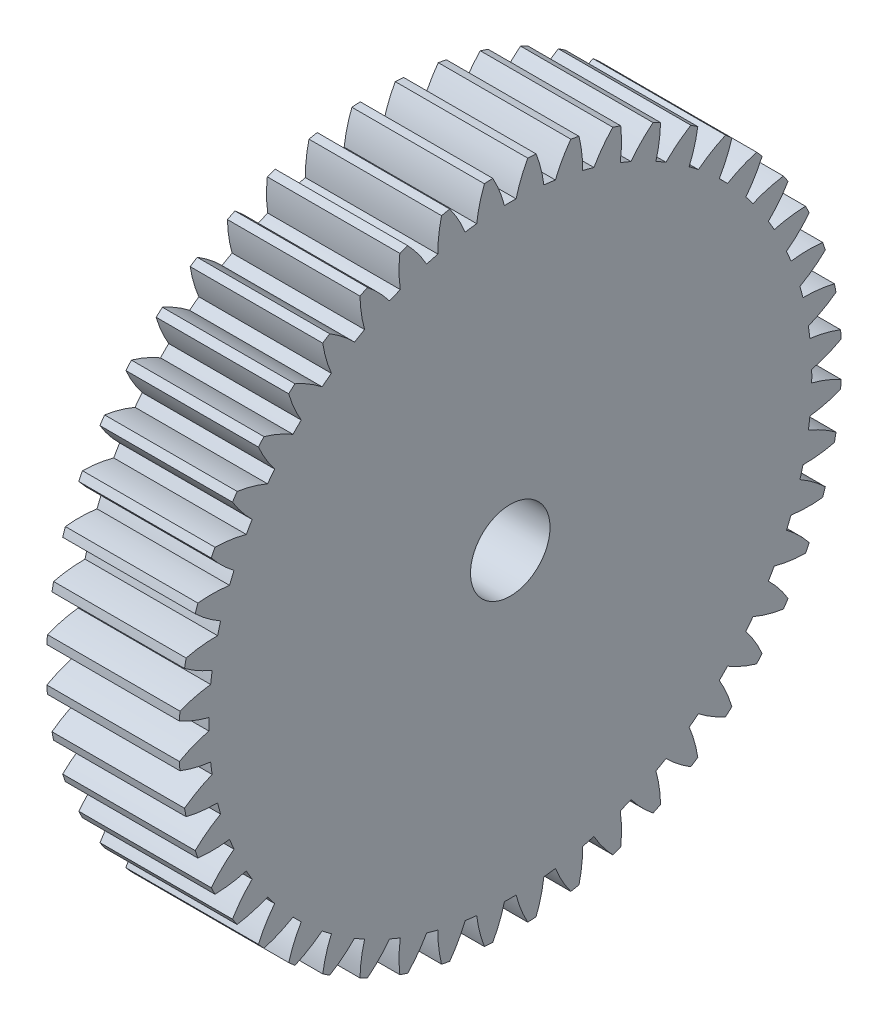
SolidWorks part; units mm, degrees
ref_plane "Plane1" through (0, 0, 0) normal (0, 0, 1) x (1, 0, 0)
ref_plane "Plane2" through (0, 0, 0) normal (0, 1, 0) x (1, 0, 0)
ref_plane "Plane3" through (0, 0, 0) normal (1, 0, 0) x (0, 0, -1)
other "Configuration Table"
sketch "HoldingSke" plane through (0, 0, 0) normal (0, 1, 0) x (1, 0, 0)
  line L0 (0, 0) -> (0.6691, -0.7431)
  line L1 (-15, 0) -> (100, 0) construction
  line L2 (0, 0) -> (-2.1039, 2.3779)
  line L3 (0, 0) -> (-11.863, 4.5341)
  line L4 (0, 0) -> (5.7786, 6.4178)
  line L5 (0, 0) -> (-46.8476, -17.4728)
  line L6 (0, 0) -> (-8.2896, -5.593)
  line L7 (-2.1039, 2.3779) -> (8.6586, 51.2059)
  line L8 (-76.2, 54.61) -> (-75.3, 54.61)
  line L9 (-71.009, 38.7566) -> (-53.1078, 45.2721)
  line L10 (-76.2, 71.12) -> (104.1128, 71.12)
  line L11 (0, 0) -> (-10, 0)
  line L12 (-76.2, 101.6) -> (-76.162, 101.6)
  line L13 (24.9733, 27.94) -> (52.9518, 28.4284)
  line L14 (24.9733, 27.94) -> (24.9743, 27.94)
  line L15 (24.9733, 27.94) -> (100.4006, 29.5858)
  line L16 (-63.627, -1) -> (-12.827, -1)
  circle A0 centre (0, 0) radius 2.5
  circle A1 centre (0, 0) radius 22.749
  circle A2 centre (0, 0) radius 37.5
  circle A3 centre (0, 0) radius 2.5
  dimension "MHD" = 45.498
  dimension "Hub_dia" = 75
  dimension "Bore" = 5
  dimension "MBD" = 5
  dimension "Num_teeth" = 48
  dimension "Pitch" = 1
  dimension "Overall_len" = 50
  dimension "Show_teeth" = 48
  dimension "Thickness" = 10
  dimension "OAL" = 50.0001
  dimension "T_dim" = 0.9
  dimension "Ap" = 20
  dimension "H" = 19.05
  dimension "Pitch_radius" = 180.3128
  dimension "Width" = 10
  dimension "Backlash" = 0.038
  dimension "Addendum_fac" = 1
  dimension "Dedendum_fac" = 1.25
  dimension "Clearance_fac" = 0.25
  dimension "Dedendum_add" = 0.001
  dimension "Module" = 1
sketch "BasProSke" plane through (0, 0, 0) normal (0, 1, 0) x (1, 0, 0)
  line L0 (-10, 0) -> (60, 0) construction
  line L1 (0, 0) -> (0, 25)
  line L2 (0, 0) -> (10, 0)
  line L3 (10, 0) -> (10, 25)
  line L4 (10, 25) -> (0, 25)
  dimension "Thickness" = 10
  dimension "Diameter" = 50
revolve "Base-Revolve" add sketch "BasProSke" angle 360 about L0
sketch "TooCutSke" plane through (0, 0, 0) normal (1, 0, 0) x (0, 0, -1)
  line L1 (0, 0) -> (0, 107) construction
  line L2 (0, 0) -> (-0.8518, 23.9849) construction
  line L3 (0, 0) -> (-3.1379, 47.8757) construction
  line L4 (-0.8518, 23.9849) -> (-1.569, 23.9379) construction
  arc A0 (0.4395, 22.7448) -> (-0.4395, 22.7448) centre (0, 0) ccw
  arc A1 (1.3336, 24.9898) -> (-1.3336, 24.9898) centre (0, 0) ccw
  circle A2 centre (0, 0) radius 24 construction
  circle A3 centre (0, 0) radius 22.5526 construction
  arc A4 (-0.4395, 22.7448) -> (-1.3336, 24.9898) centre (-9.7344, 20.3436) ccw
  arc A5 (1.3336, 24.9898) -> (0.4395, 22.7448) centre (9.7344, 20.3436) ccw
  dimension "Root_dia" = 45.498
  dimension "Overcut_dia" = 50.0508
  dimension "Pitch_dia" = 48
  dimension "Base_dia" = 45.1052
  dimension "Flank_rad" = 9.6
  dimension "Half_ang" = 3.75
  dimension "Half_CT" = 0.7188
extrude "ToothCut" cut sketch "TooCutSke" along normal through all
fillet "Breaks" [suppressed] radius 0.02
fillet "RootFillets" [suppressed] radius 0.251
pattern_circular "TeethCuts" count 48 every 7.5 about axis through (-10, 0, 0) along (1, 0, 0) of "ToothCut", "RootFillets", "Breaks"
sketch "HubNeaOneSke" plane through (0, 0, 0) normal (-1, 0, 0) x (0, 0, 1)
  circle A0 centre (0, 0) radius 22.749
  dimension "Diameter" = 45.498
extrude "HubNearOne" [suppressed] add sketch "HubNeaOneSke" along normal blind 40.0001
sketch "HubNeaBotSke" plane through (0, 0, 0) normal (-1, 0, 0) x (0, 0, 1)
  circle A0 centre (0, 0) radius 22.749
  dimension "Diameter" = 45.498
extrude "HubNearBoth" [suppressed] add sketch "HubNeaBotSke" along normal blind 20
ref_plane "FarPln" through (10, 0, 0) normal (1, 0, 0) x (0, 0, -1)
sketch "HubFarSke" plane through (10, 0, 0) normal (1, 0, 0) x (0, 0, -1)
  circle A0 centre (0, 0) radius 22.749
  dimension "Diameter" = 45.498
extrude "HubFar" [suppressed] add sketch "HubFarSke" along normal blind 20
sketch "BorSke" plane through (0, 0, 0) normal (1, 0, 0) x (0, 0, -1)
  circle A0 centre (0, 0) radius 2.5
  dimension "Diameter" = 5
extrude "Bore" cut sketch "BorSke" along normal mid plane 100.0001
sketch "KeySke" plane through (0, 0, 0) normal (1, 0, 0) x (0, 0, -1)
  line L0 (-1, 0) -> (-1, 3.4)
  line L1 (-1, 3.4) -> (1, 3.4)
  line L2 (1, 3.4) -> (1, 0)
  line L3 (0, 0) -> (0, 34) construction
  line L4 (-1, 0) -> (1, 0)
  dimension "Offset" = 3.4
  dimension "Width" = 2
extrude "Keyway" [suppressed] cut sketch "KeySke" along normal mid plane 100.0001
pattern_circular "Keyway2" [suppressed] count 2 every 90 about axis through (-10, 0, 0) along (1, 0, 0)
sketch "Sketch1" plane through (10, 0, 0) normal (1, 0, 0) x (0, 0, -1)
  circle A0 centre (0, 0) radius 3
  dimension "D1" = 6
extrude "Cut-Extrude1" cut sketch "Sketch1" against normal through all
equation "' \"Module@HoldingSke\" = 6.35"
equation "' \"Num_teeth@HoldingSke\" = 12"
equation "' \"Ap@HoldingSke\" =  20"
equation "' \"Ap@HoldingSke\" = 20"
equation "' \"Width@HoldingSke\" = 0.5 * 25.4"
equation "' \"Hub_dia@HoldingSke\"= 1 * 25.4"
equation "' \"Hub_dia@HoldingSke\" = 1 * 25.4"
equation "' \"Overall_len@HoldingSke\" = 1.0 * 25.4"
equation "' \"Bore@HoldingSke\" = 0.75 * 25.4"
equation "' \"T_dim@HoldingSke\" = 0.1 * 25.4"
equation "' \"Width@KeySke\" = 0.25 * 25.4"
equation "' \"Show_teeth@HoldingSke\" = 13"
equation "' \"Backlash@HoldingSke\" = 0.009 * 25.4"
equation "' \"Addendum_fac@HoldingSke\" = 1.0"
equation "' \"Dedendum_fac@HoldingSke\" = 1.25"
equation "' \"Dedendum_add@HoldingSke\" = 0.00005 * 25.4"
equation "' \"Clearance_fac@HoldingSke\" = 0.25"
equation "\"Pitch@HoldingSke\" = 1 / \"Module@HoldingSke\""
equation "\"Overcut_dia@TooCutSke\" = (\"Num_teeth@HoldingSke\" + 2 * \"Addendum_fac@HoldingSke\") / \"Pitch@HoldingSke\" + 0.002 * 25.4"
equation "\"Pitch_dia@TooCutSke\" = \"Num_teeth@HoldingSke\" / \"Pitch@HoldingSke\""
equation "\"Base_dia@TooCutSke\" = \"Num_teeth@HoldingSke\" / \"Pitch@HoldingSke\" * cos((\"Ap@HoldingSke\"  * 3.14159265 / 180))"
equation "\"Root_dia@TooCutSke\" = (\"Num_teeth@HoldingSke\" + 2) / \"Pitch@HoldingSke\" - 2 * (\"Addendum_fac@HoldingSke\" + \"Dedendum_fac@HoldingSke\") / \"Pitch@HoldingSke\" - \"Dedendum_add@HoldingSke\" * 2"
equation "\"Half_ang@TooCutSke\" = 180 / \"Num_teeth@HoldingSke\""
equation "\"Half_CT@TooCutSke\" = \"Num_teeth@HoldingSke\" / \"Pitch@HoldingSke\" * sin((3.14159265 / 2 / \"Num_teeth@HoldingSke\")) / 2 - 7 * \"Backlash@HoldingSke\" / 4"
equation "\"Flank_rad@TooCutSke\" = \"Num_teeth@HoldingSke\" / \"Pitch@HoldingSke\" / 5"
equation "\"Radius@RootFillets\" = \"Clearance_fac@HoldingSke\" / \"Pitch@HoldingSke\" + \"Dedendum_add@HoldingSke\""
equation "\"Break_rad@Breaks\" = 0.02 / \"Pitch@HoldingSke\""
equation "\"Thickness@HoldingSke\" = \"Width@HoldingSke\""
equation "\"OAL@HoldingSke\" = \"Thickness@HoldingSke\""
equation "\"MHD@HoldingSke\" = (\"Num_teeth@HoldingSke\" + 2) / \"Pitch@HoldingSke\" - 2 * (\"Addendum_fac@HoldingSke\" + \"Dedendum_fac@HoldingSke\")  / \"Pitch@HoldingSke\" - \"Dedendum_add@HoldingSke\" * 2"
equation "\"MBD@HoldingSke\" = (\"Num_teeth@HoldingSke\" + 2) / \"Pitch@HoldingSke\" - 2 * (\"Addendum_fac@HoldingSke\" + \"Dedendum_fac@HoldingSke\")  / \"Pitch@HoldingSke\" - \"Dedendum_add@HoldingSke\" * 2 - 0.002 * 25.4"
equation "\"MHD@HoldingSke\" = ((sgn( \"MHD@HoldingSke\" - \"Hub_dia@HoldingSke\" )-1)*( \"MHD@HoldingSke\" - \"Hub_dia@HoldingSke\" ))/-2+ \"Hub_dia@HoldingSke\""
equation "\"MBD@HoldingSke\" = ((sgn( \"MBD@HoldingSke\" - \"Bore@HoldingSke\" )-1)*( \"MBD@HoldingSke\" - \"Bore@HoldingSke\" ))/-2+ \"Bore@HoldingSke\""
equation "\"OAL@HoldingSke\" = ((sgn( \"OAL@HoldingSke\" - \"Overall_len@HoldingSke\" )+1)*( \"OAL@HoldingSke\" - \"Overall_len@HoldingSke\" ))/2 + \"Overall_len@HoldingSke\" + 0.000002 * 25.4"
equation "\"Num_teeth@TeethCuts\" = int( \"Show_teeth@HoldingSke\" ) + 1"
equation "\"Num_teeth@TeethCuts\" = ((sgn( \"Num_teeth@TeethCuts\" - \"Num_teeth@HoldingSke\" )-1)*( \"Num_teeth@TeethCuts\" - \"Num_teeth@HoldingSke\" ))/-2+ \"Num_teeth@HoldingSke\""
equation "\"Num_teeth@TeethCuts\" = ((sgn( \"Num_teeth@TeethCuts\" - 2.0)+1)*( \"Num_teeth@TeethCuts\" - 2.0))/2 +2.0"
equation "\"Angle@TeethCuts\" = 360.0 / \"Num_teeth@HoldingSke\""
equation "\"Diameter@BasProSke\" = (\"Num_teeth@HoldingSke\" + 2 * \"Addendum_fac@HoldingSke\") / \"Pitch@HoldingSke\""
equation "\"Thickness@BasProSke\"  = \"Thickness@HoldingSke\""
equation "' \"Fillet_rad@BasProSke\" =  \"Thickness@HoldingSke\" * 0.05"
equation "' \"Fillet_rad@BasProSke\" = \"Thickness@HoldingSke\" * 0.05"
equation "\"MHD@HoldingSke\" = ((sgn( \"MHD@HoldingSke\" - \"Root_dia@TooCutSke\" )-1)*( \"MHD@HoldingSke\" - \"Root_dia@TooCutSke\" ))/-2+ \"Root_dia@TooCutSke\""
equation "\"Diameter@HubNeaOneSke\" = \"MHD@HoldingSke\""
equation "\"Length@HubNearOne\" = \"OAL@HoldingSke\" - \"Thickness@BasProSke\""
equation "\"Diameter@HubNeaBotSke\" = \"MHD@HoldingSke\""
equation "\"Length@HubNearBoth\" = ( \"OAL@HoldingSke\" - \"Thickness@BasProSke\" ) / 2.0"
equation "\"Thickness@FarPln\" = \"Thickness@BasProSke\""
equation "\"Diameter@HubFarSke\" = \"MHD@HoldingSke\""
equation "\"Length@HubFar\" = ( \"OAL@HoldingSke\" - \"Thickness@BasProSke\" ) / 2.0"
equation "\"Diameter@BorSke\" = \"MBD@HoldingSke\""
equation "\"D1@Bore\" = \"OAL@HoldingSke\" * 2.0"
equation "\"D1@Keyway\" = \"OAL@HoldingSke\" * 2.0"
equation "\"Offset@KeySke\" = \"T_dim@HoldingSke\" + \"MBD@HoldingSke\" / 2.0"
